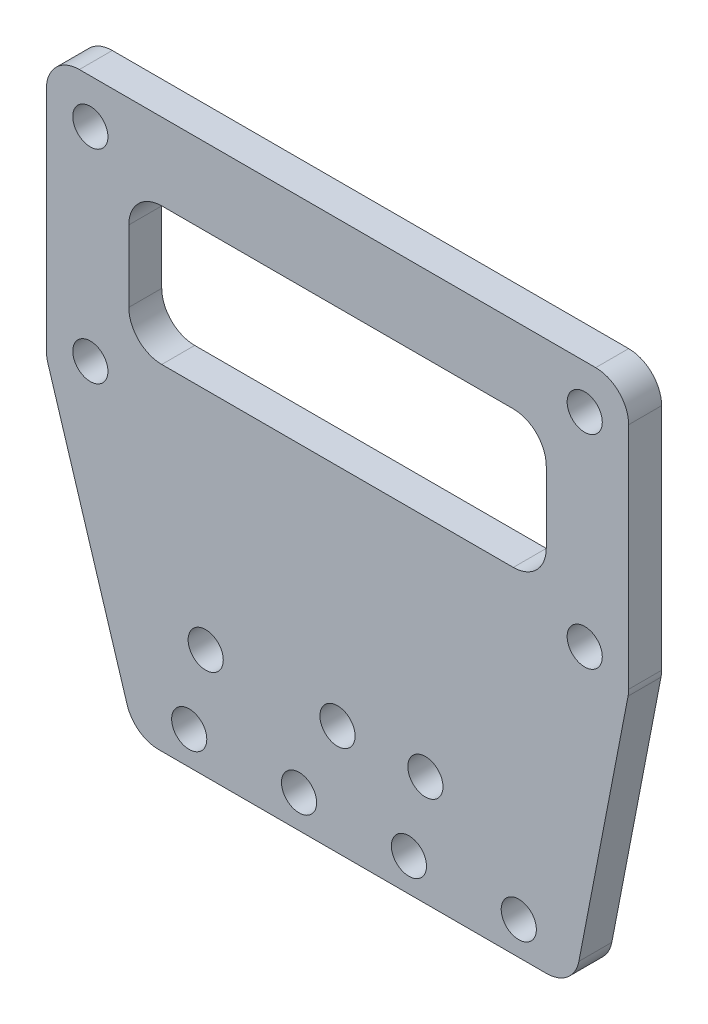
SolidWorks part; units mm, degrees
material "Hexcel AS4C (3000 丝)"
ref_plane "前视基准面" through (0, 0, 0) normal (0, 0, 1) x (1, 0, 0)
ref_plane "上视基准面" through (0, 0, 0) normal (0, 1, 0) x (1, 0, 0)
ref_plane "右视基准面" through (0, 0, 0) normal (1, 0, 0) x (0, 0, -1)
sketch "草图1" plane through (0, 0, 0) normal (0, 0, 1) x (1, 0, 0)
  line L0 (-40, 0) -> (-48, 25.8556)
  line L1 (0, 0) -> (-40, 0)
  line L5 (1, 46) -> (-44, 46) construction
  line L6 (1, 46) -> (1, 27.5) construction
  line L7 (1, 27.5) -> (-44, 27.5) construction
  line L8 (-44, 46) -> (-44, 27.5) construction
  line L9 (1, 46) -> (-44, 27.5) construction
  line L10 (1, 27.5) -> (-44, 46) construction
  line L11 (-48, 25.8556) -> (-48, 50)
  line L13 (7, -1.4222) -> (7, 51.7153) construction
  line L16 (-48, 50) -> (5, 50)
  line L17 (5, 50) -> (5, 25.8556)
  line L18 (5, 25.8556) -> (0, 0)
  circle A0 centre (-44, 46) radius 1.6
  circle A1 centre (1, 46) radius 1.6
  circle A2 centre (1, 27.5) radius 1.6
  circle A3 centre (-44, 27.5) radius 1.6
  point P5 (-21.5, 36.75)
  point P18 (-44, 36.75)
  dimension "D5" = 3.2
  dimension "D1" = 27.5
  dimension "D2" = 40
  dimension "D3" = 18.5
  dimension "D4" = 45
  dimension "D6" = 7
  dimension "D7" = 4
  dimension "D8" = 6
  dimension "D9" = 4
  dimension "D10" = 4
extrude "凸台-拉伸1" add sketch "草图1" along normal blind 3
sketch "草图2" plane through (0, 0, 3) normal (0, 0, 1) x (1, 0, 0)
  line L1 (-5, 3) -> (-15, 3) construction
  line L2 (-40, 0) -> (0, 0) construction
  circle A0 centre (-5, 3) radius 1.6
  circle A1 centre (-15, 3) radius 1.6
  circle A2 centre (-25, 3) radius 1.6
  circle A3 centre (-35, 3) radius 1.6
  dimension "D1" = 5
  dimension "D2" = 3.2
  dimension "D3" = 3
  dimension "D5" = 10
  dimension "D4" = 4
extrude "切除-拉伸1" cut sketch "草图2" against normal through all
sketch "草图3" plane through (0, 0, 3) normal (0, 0, 1) x (1, 0, 0)
  line L0 (-40, 0) -> (0, 0) construction
  line L1 (31, 53.5) -> (-10, 53.5) construction
  line L2 (31, 53.5) -> (31, 14.5) construction
  line L3 (31, 14.5) -> (-10, 14.5) construction
  line L4 (-10, 53.5) -> (-10, 14.5) construction
  line L5 (31, 53.5) -> (-10, 14.5) construction
  line L6 (31, 14.5) -> (-10, 53.5) construction
  line L7 (-44, 46) -> (1, 46) construction
  line L8 (28.5, 52) -> (-7.5, 52) construction
  line L9 (28.5, 52) -> (28.5, 16) construction
  line L10 (28.5, 16) -> (-7.5, 16) construction
  line L11 (-7.5, 52) -> (-7.5, 16) construction
  line L12 (28.5, 52) -> (-7.5, 16) construction
  line L13 (28.5, 16) -> (-7.5, 52) construction
  line L14 (-21.5, 34) -> (-21.5, 10) construction
  line L15 (-21.5, 10) -> (-33.5, 10) construction
  line L16 (-33.5, 10) -> (-21.5, 34) construction
  circle A0 centre (-13.5, 10) radius 1.6
  circle A1 centre (-7.5, 52) radius 1.35 construction
  circle A2 centre (28.5, 52) radius 1.35 construction
  circle A3 centre (-7.5, 16) radius 1.35 construction
  circle A4 centre (28.5, 16) radius 1.35 construction
  circle A5 centre (-21.5, 10) radius 1.6
  circle A6 centre (-33.5, 10) radius 1.6
  circle A7 centre (-21.5, 34) radius 1.6
  point P0 (10.5, 34)
  point P5 (10.5, 34)
  point P29 (-21.5, 46)
  dimension "D5" = 2.7
  dimension "D6" = 3.2
  dimension "D9" = 10
  dimension "D11" = 20
  dimension "D1" = 39
  dimension "D2" = 41
  dimension "D3" = 36
  dimension "D4" = 36
  dimension "D7" = 24
  dimension "D8" = 12
  dimension "D10" = 32
extrude "切除-拉伸2" cut sketch "草图3" against normal through all
sketch "草图4" plane through (0, 0, 3) normal (0, 0, 1) x (1, 0, 0)
  line L1 (-40.5, 43) -> (-2.5, 43)
  line L2 (-44, 46) -> (1, 46) construction
  line L3 (-44, 46) -> (-44, 27.5) construction
  line L4 (-44, 27.5) -> (1, 27.5) construction
  line L5 (1, 46) -> (1, 27.5) construction
  line L6 (-21.5, 27.5) -> (-21.5, 46) construction
  line L7 (-44, 36.75) -> (1, 36.75) construction
  line L8 (-40.5, 43) -> (-40.5, 30.5)
  line L9 (-40.5, 30.5) -> (-2.5, 30.5)
  line L10 (-2.5, 43) -> (-2.5, 30.5)
  line L11 (-21.5, 30.5) -> (-21.5, 43) construction
  line L12 (-40.5, 36.75) -> (-2.5, 36.75) construction
  point P0 (-21.5, 36.75)
  point P425 (-21.5, 36.75)
  dimension "4" = 3
  dimension "3" = 3.5
extrude "切除-拉伸3" cut sketch "草图4" against normal through all
fillet "圆角1" radius 3 10 edges at (-48, 25.8556, 1.5) (-40, 0, 1.5) (0, 0, 1.5) (5, 25.8556, 1.5) (5, 50, 1.5) (-48, 50, 1.5) (-2.5, 30.5, 1.5) (-2.5, 43, 1.5) (-40.5, 43, 1.5) (-40.5, 30.5, 1.5)
